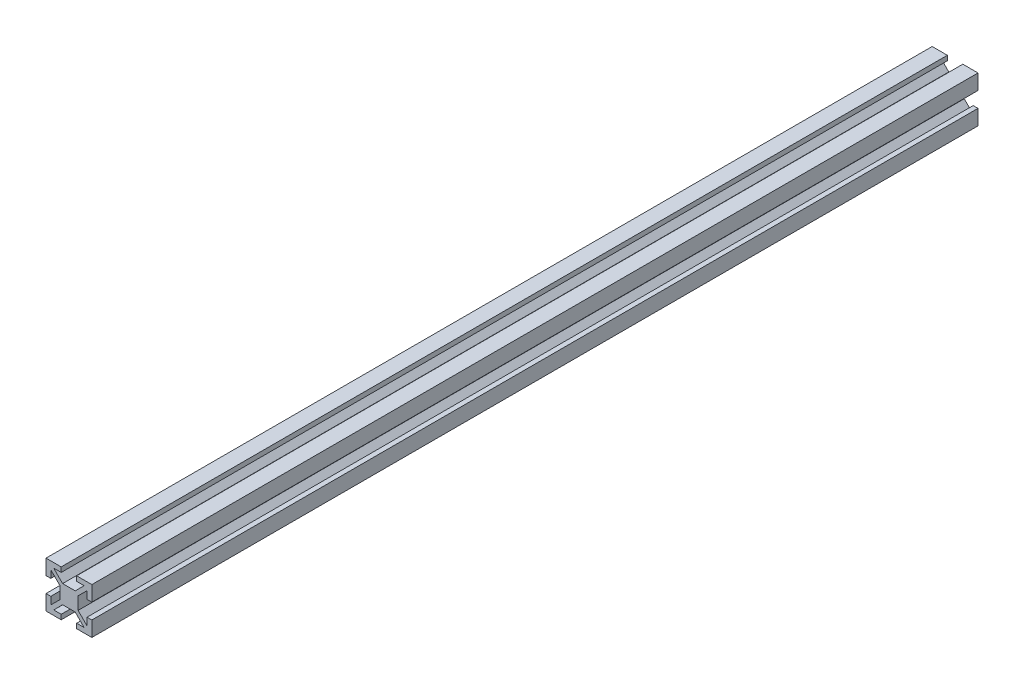
SolidWorks part; units mm, degrees
ref_plane "Front Plane" through (0, 0, 0) normal (0, 0, 1) x (1, 0, 0)
ref_plane "Top Plane" through (0, 0, 0) normal (0, 1, 0) x (1, 0, 0)
ref_plane "Right Plane" through (0, 0, 0) normal (1, 0, 0) x (0, 0, -1)
sketch "Sketch1" plane through (0, 0, 0) normal (0, 0, 1) x (1, 0, 0)
  line L0 (-7.5, 7.5) -> (-2.5307, 7.5)
  line L1 (-7.5, -7.5) -> (7.5, -7.5) construction
  line L2 (-7.5, -7.5) -> (-7.5, 7.5) construction
  line L3 (-7.5, 7.5) -> (7.5, 7.5) construction
  line L4 (7.5, -7.5) -> (7.5, 7.5) construction
  line L5 (-7.5, -7.5) -> (7.5, 7.5) construction
  line L6 (-7.5, 7.5) -> (7.5, -7.5) construction
  line L7 (-2.5307, 7.5) -> (-2.5307, 5.9245)
  line L8 (-2.5307, 5.9245) -> (-4.9716, 5.9245)
  line L9 (-4.9716, 5.9245) -> (-2.0693, 3)
  line L10 (-2.0693, 3) -> (2.0693, 3)
  line L11 (0, -55) -> (0, 55) construction
  line L12 (-3, 2.0693) -> (-3, -2.0693)
  line L13 (-7.5, 2.5307) -> (-5.9245, 2.5307)
  line L14 (-5.9245, 2.5307) -> (-5.9245, 4.9716)
  line L15 (-5.9245, 4.9716) -> (-3, 2.0693)
  line L16 (-7.5, 7.5) -> (-7.5, 2.5307)
  line L17 (55, 0) -> (-55, 0) construction
  line L18 (-7.5, -2.5307) -> (-5.9245, -2.5307)
  line L19 (-5.9245, -2.5307) -> (-5.9245, -4.9716)
  line L20 (-5.9245, -4.9716) -> (-3, -2.0693)
  line L21 (-2.0693, -3) -> (2.0693, -3)
  line L22 (-4.9716, -5.9245) -> (-2.0693, -3)
  line L23 (-2.5307, -5.9245) -> (-4.9716, -5.9245)
  line L24 (-2.5307, -7.5) -> (-2.5307, -5.9245)
  line L25 (-7.5, -7.5) -> (-2.5307, -7.5)
  line L26 (-7.5, -7.5) -> (-7.5, -2.5307)
  line L27 (7.5, -7.5) -> (7.5, -2.5307)
  line L28 (7.5, -7.5) -> (2.5307, -7.5)
  line L29 (2.5307, -7.5) -> (2.5307, -5.9245)
  line L30 (2.5307, -5.9245) -> (4.9716, -5.9245)
  line L31 (4.9716, -5.9245) -> (2.0693, -3)
  line L32 (5.9245, -4.9716) -> (3, -2.0693)
  line L33 (5.9245, -2.5307) -> (5.9245, -4.9716)
  line L34 (7.5, -2.5307) -> (5.9245, -2.5307)
  line L35 (7.5, 7.5) -> (7.5, 2.5307)
  line L36 (5.9245, 4.9716) -> (3, 2.0693)
  line L37 (5.9245, 2.5307) -> (5.9245, 4.9716)
  line L38 (7.5, 2.5307) -> (5.9245, 2.5307)
  line L39 (3, 2.0693) -> (3, -2.0693)
  line L40 (4.9716, 5.9245) -> (2.0693, 3)
  line L41 (2.5307, 5.9245) -> (4.9716, 5.9245)
  line L42 (2.5307, 7.5) -> (2.5307, 5.9245)
  line L43 (7.5, 7.5) -> (2.5307, 7.5)
  point P0 (0, 0)
  point P21 (-3, 0)
  point P34 (0, -3)
  point P42 (0, 3)
  point P45 (3, 0)
  dimension "D1" = 15
  dimension "D2" = 6
extrude "Boss-Extrude1" add sketch "Sketch1" along normal mid plane 290
